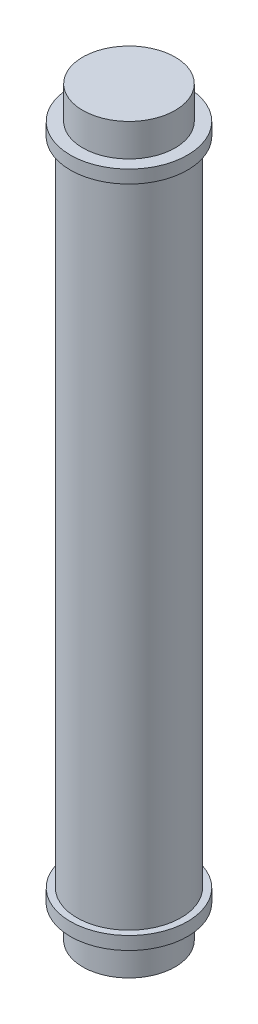
SolidWorks part; units mm, degrees
material "6061 합금"
ref_plane "정면" through (0, 0, 0) normal (0, 0, 1) x (1, 0, 0)
ref_plane "윗면" through (0, 0, 0) normal (0, 1, 0) x (1, 0, 0)
ref_plane "우측면" through (0, 0, 0) normal (1, 0, 0) x (0, 0, -1)
sketch "스케치1" plane through (0, 0, 0) normal (0, 1, 0) x (1, 0, 0)
  circle A0 centre (0, 0) radius 2
  circle A1 centre (0, 0) radius 1.5
  dimension "D1" = 4
  dimension "D2" = 3
extrude "보스-돌출1" add sketch "스케치1" along normal mid plane 25
sketch "스케치2" plane through (0, 12.5, 0) normal (0, 1, 0) x (1, 0, 0)
  circle A0 centre (0, 0) radius 2.25
  dimension "D1" = 4.5
extrude "보스-돌출2" add sketch "스케치2" along normal blind 0.5
sketch "스케치3" plane through (0, 13, 0) normal (0, 1, 0) x (1, 0, 0)
  circle A0 centre (0, 0) radius 1.775
  dimension "D1" = 3.55
extrude "보스-돌출3" add sketch "스케치3" along normal blind 1.25
mirror "대칭 복사1" about plane through (0, 0, 0) normal (0, 1, 0) of "보스-돌출2", "보스-돌출3"
